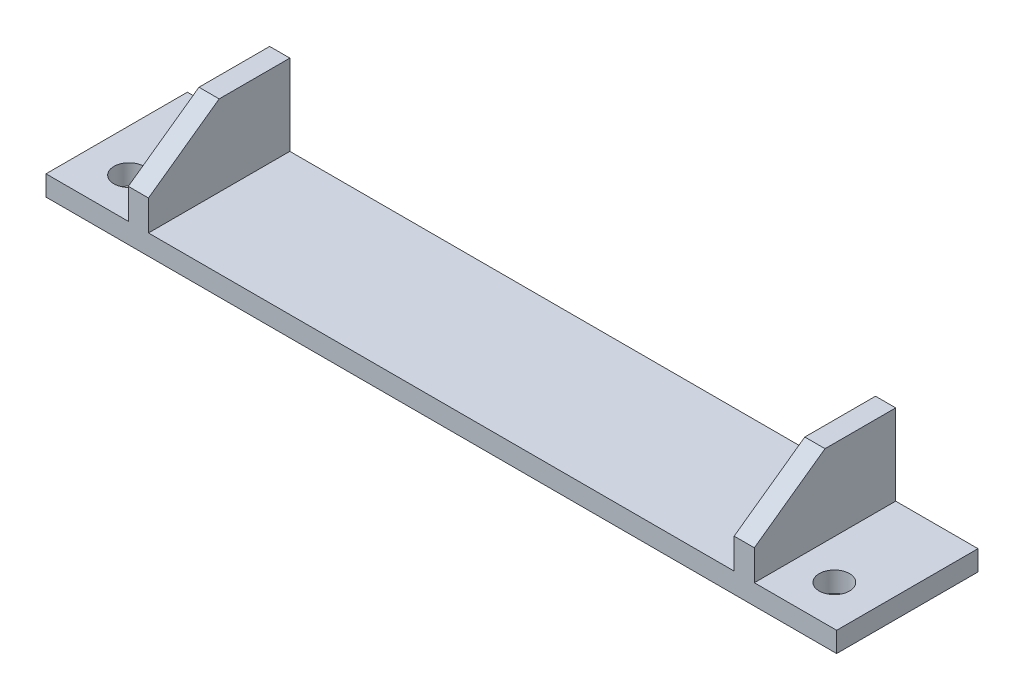
SolidWorks part; units mm, degrees
ref_plane "Front Plane" through (0, 0, 0) normal (0, 0, 1) x (1, 0, 0)
ref_plane "Top Plane" through (0, 0, 0) normal (0, 1, 0) x (1, 0, 0)
ref_plane "Right Plane" through (0, 0, 0) normal (1, 0, 0) x (0, 0, -1)
sketch "Sketch1" plane through (0, 0, 0) normal (0, 1, 0) x (1, 0, 0)
  line L1 (-29.4504, 10.8328) -> (48.8496, 10.8328)
  line L2 (-29.4504, 10.8328) -> (-29.4504, -3.1672)
  line L3 (-29.4504, -3.1672) -> (48.8496, -3.1672)
  line L4 (48.8496, 10.8328) -> (48.8496, -3.1672)
  line L30 (-46.7592, 30.8012) -> (-25.7592, 30.8012) construction
  line L31 (-50.2339, 19.9) -> (-29.2339, 19.9) construction
  line L32 (9.6996, 10.8328) -> (9.6996, 3.9136) construction
  line L38 (24.6996, 0.9136) -> (-5.3004, 6.9136) construction
  line L39 (24.6996, 6.9136) -> (-5.3004, 0.9136) construction
  dimension "D1" = 78.3
  dimension "D2" = 14
  dimension "D3" = 30
  dimension "D4" = 6
extrude "Boss-Extrude1" add sketch "Sketch1" along normal blind 2 contours L2 L1 L4 L3
sketch "Sketch3" plane through (0, 2, 0) normal (0, 1, 0) x (1, 0, 0)
  line L0 (9.6996, 10.8328) -> (-27.7654, 10.8328) construction
  line L1 (-29.4504, 10.8328) -> (48.8496, 10.8328) construction
  line L2 (9.6996, 10.8328) -> (47.1646, 10.8328) construction
  line L3 (-27.7654, 10.8328) -> (-27.7654, -1.8672) construction
  line L4 (-27.7654, -1.8672) -> (47.1646, -1.8672) construction
  line L5 (47.1646, -1.8672) -> (47.1646, 10.8328) construction
  line L6 (44.6246, 0.8328) -> (-25.2254, 0.8328) construction
  line L7 (9.6996, 10.8328) -> (9.6996, 0.8328) construction
  circle A1 centre (-25.2254, 0.8328) radius 1.5
  circle A2 centre (44.6246, 0.8328) radius 1.5
  point P13 (9.6996, 0.8328)
extrude "Cut-Extrude2" cut sketch "Sketch3" against normal through all both and the other way through all contours A1 | A2
sketch "Sketch5" plane through (0, 0, 0) normal (0, -1, 0) x (1, 0, 0)
  line L0 (9.6996, 3.1672) -> (-9.5004, 3.1672) construction
  line L1 (-29.4504, 3.1672) -> (48.8496, 3.1672) construction
  line L2 (9.6996, 3.1672) -> (28.8996, 3.1672) construction
  line L3 (9.6996, 3.1672) -> (9.6996, -10.8328) construction
  line L4 (-29.4504, -10.8328) -> (48.8496, -10.8328) construction
  line L13 (-9.5004, 3.1672) -> (-9.5004, -10.8328) construction
  line L14 (28.8996, 3.1672) -> (28.8996, -10.8328) construction
  line L16 (-9.5004, -10.8328) -> (-12.5004, -10.8328)
  line L17 (-9.5004, -10.8328) -> (-9.5004, -7.8328)
  line L18 (-9.5004, -7.8328) -> (-12.5004, -7.8328)
  line L19 (-12.5004, -10.8328) -> (-12.5004, -7.8328)
  line L20 (28.8996, -10.8328) -> (31.8996, -10.8328)
  line L21 (28.8996, -10.8328) -> (28.8996, -7.8328)
  line L22 (28.8996, -7.8328) -> (31.8996, -7.8328)
  line L23 (31.8996, -10.8328) -> (31.8996, -7.8328)
  dimension "D1" = 3
  dimension "D2" = 3
  dimension "D3" = 3
  dimension "D4" = 3
extrude "Boss-Extrude2" add sketch "Sketch5" along normal blind 2
sketch "Sketch7" plane through (0, 2, 0) normal (0, 1, 0) x (1, 0, 0)
  line L0 (9.6996, 10.8328) -> (9.6996, -3.1672) construction
  line L1 (-29.4504, 10.8328) -> (48.8496, 10.8328) construction
  line L2 (-29.4504, -3.1672) -> (48.8496, -3.1672) construction
  line L3 (38.6996, 10.8328) -> (38.6996, -3.1672)
  line L4 (-19.3004, 10.8328) -> (-21.3004, 10.8328)
  line L5 (9.6996, 10.8328) -> (-19.3004, 10.8328) construction
  line L6 (9.6996, 10.8328) -> (38.6996, 10.8328) construction
  line L15 (-19.3004, 10.8328) -> (-19.3004, -3.1672)
  line L16 (-19.3004, -3.1672) -> (-21.3004, -3.1672)
  line L17 (-21.3004, 10.8328) -> (-21.3004, -3.1672)
  line L18 (38.6996, 10.8328) -> (40.6996, 10.8328)
  line L19 (40.6996, 10.8328) -> (40.6996, -3.1672)
  line L20 (38.6996, -3.1672) -> (40.6996, -3.1672)
  dimension "D1" = 2
extrude "Boss-Extrude3" add sketch "Sketch7" along normal blind 8
sketch "Sketch9" plane through (-21.3004, 0, 0) normal (-1, 0, 0) x (0, 0, 1)
  line L0 (3.1672, 10) -> (3.1672, 5)
  line L1 (3.1672, 10) -> (3.1672, 2) construction
  line L2 (3.1672, 5) -> (-3.8328, 10)
  line L3 (-10.8328, 10) -> (3.1672, 10) construction
  line L4 (-3.8328, 10) -> (3.1672, 10)
extrude "Cut-Extrude6" cut sketch "Sketch9" against normal through all both
